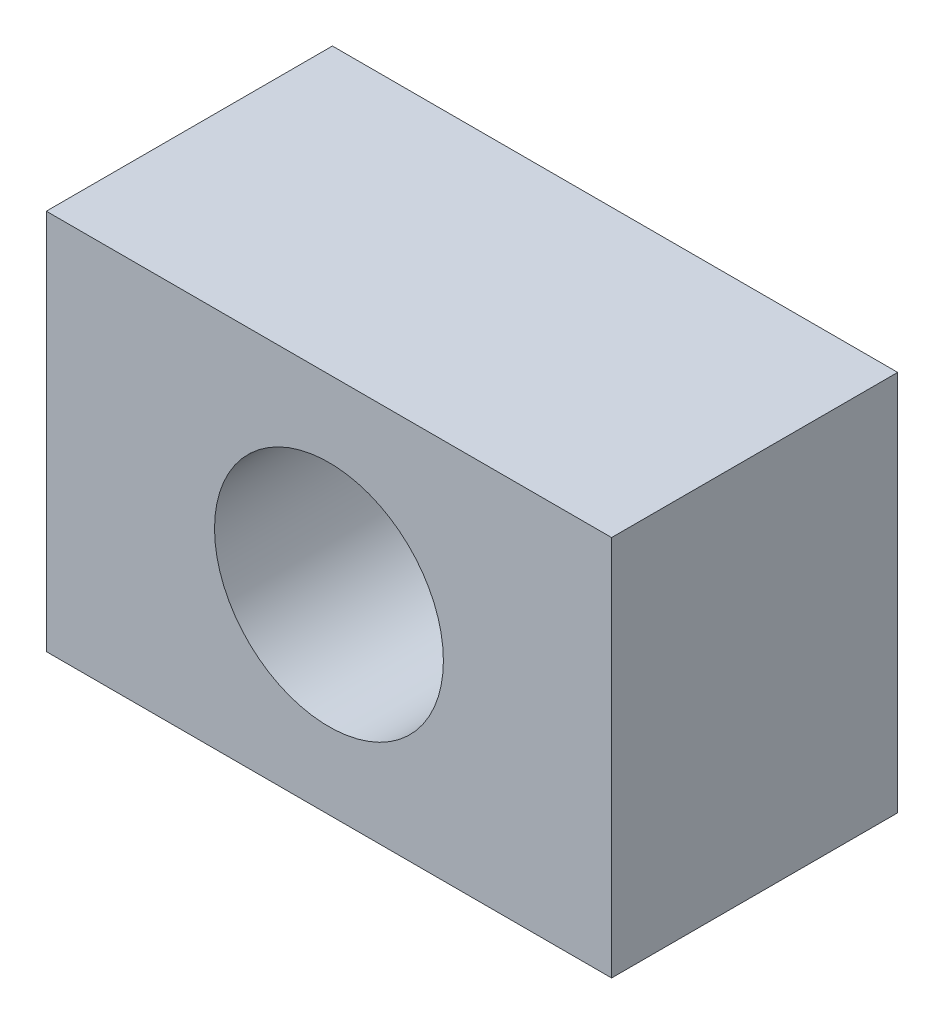
SolidWorks part; units mm, degrees
ref_plane "Front Plane" through (0, 0, 0) normal (0, 0, 1) x (1, 0, 0)
ref_plane "Top Plane" through (0, 0, 0) normal (0, 1, 0) x (1, 0, 0)
ref_plane "Right Plane" through (0, 0, 0) normal (1, 0, 0) x (0, 0, -1)
sketch "Sketch1" plane through (0, 0, 0) normal (0, 0, 1) x (1, 0, 0)
  line L1 (-14.82, -10) -> (14.82, -10)
  line L2 (-14.82, -10) -> (-14.82, 10)
  line L3 (-14.82, 10) -> (14.82, 10)
  line L4 (14.82, -10) -> (14.82, 10)
  line L5 (-14.82, -10) -> (14.82, 10) construction
  line L6 (-14.82, 10) -> (14.82, -10) construction
  circle A0 centre (0, 0) radius 6
  point P0 (0, 0)
  dimension "D3" = 12
  dimension "D1" = 14.82
  dimension "D2" = 20
extrude "Boss-Extrude1" add sketch "Sketch1" along normal blind 15
